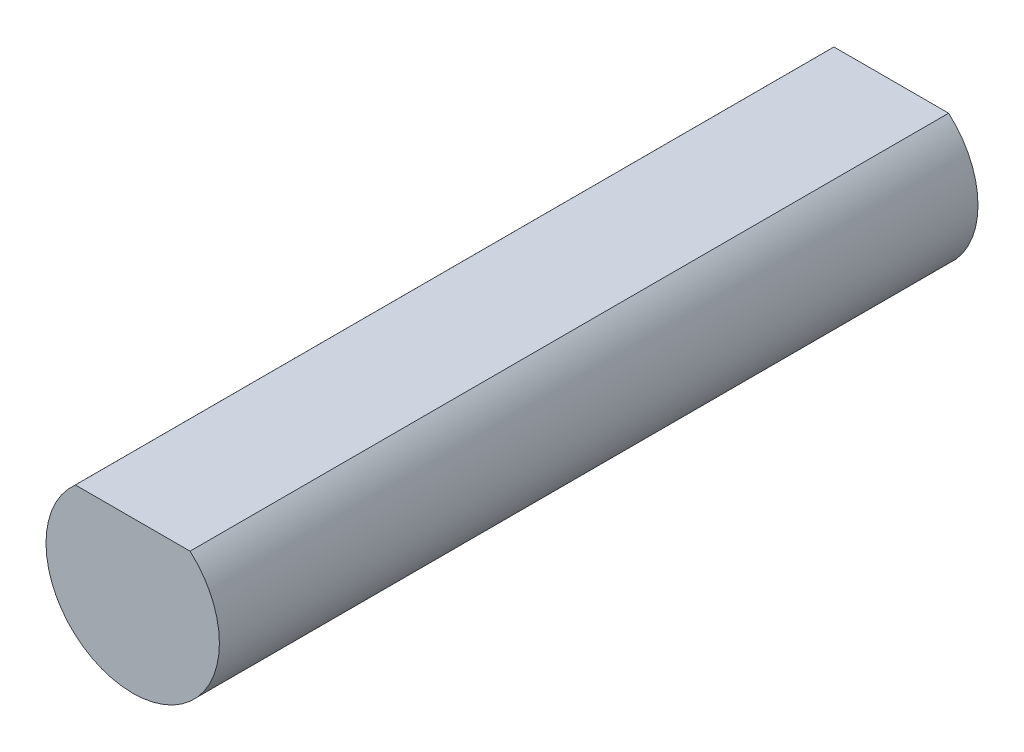
SolidWorks part; units mm, degrees
ref_plane "Front Plane" through (0, 0, 0) normal (0, 0, 1) x (1, 0, 0)
ref_plane "Top Plane" through (0, 0, 0) normal (0, 1, 0) x (1, 0, 0)
ref_plane "Right Plane" through (0, 0, 0) normal (1, 0, 0) x (0, 0, -1)
sketch "Sketch2" plane through (0, 0, 0) normal (0, 0, 1) x (1, 0, 0)
  circle A0 centre (0, 0) radius 4
  dimension "D1" = 8
extrude "Boss-Extrude1" add sketch "Sketch2" along normal blind 35
sketch "Sketch3" plane through (0, 0, 35) normal (0, 0, 1) x (1, 0, 0)
  line L0 (-2.6458, 3) -> (2.6458, 3)
  line L1 (0, 0) -> (0, 3) construction
  circle A0 centre (0, 0) radius 4 construction
  arc A1 (2.6458, 3) -> (-2.6458, 3) centre (0, 0) ccw
  dimension "D1" = 3
extrude "Cut-Extrude1" cut sketch "Sketch3" against normal up to next and the other way through all
